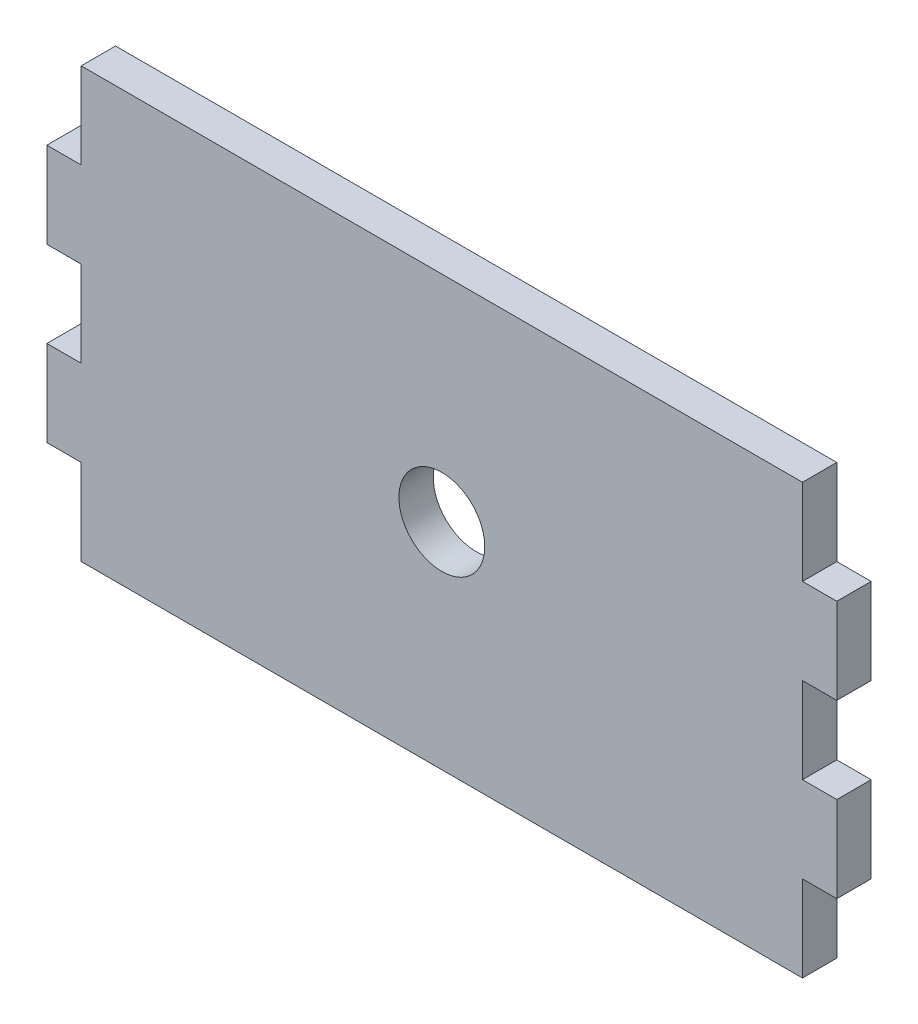
SolidWorks part; units mm, degrees
ref_plane "Front Plane" through (0, 0, 0) normal (0, 0, 1) x (1, 0, 0)
ref_plane "Top Plane" through (0, 0, 0) normal (0, 1, 0) x (1, 0, 0)
ref_plane "Right Plane" through (0, 0, 0) normal (1, 0, 0) x (0, 0, -1)
sketch "Sketch1" plane through (0, 0, 0) normal (0, 0, 1) x (1, 0, 0)
  line L0 (-46, 5) -> (-46, 15)
  line L1 (-42, -25) -> (42, -25)
  line L2 (-46, -15) -> (-46, -5)
  line L3 (-42, 25) -> (42, 25)
  line L5 (0, 25) -> (0, -25) construction
  line L6 (42, -15) -> (42, -25)
  line L7 (46, -15) -> (42, -15)
  line L8 (42, 5) -> (42, -5)
  line L9 (-46, 15) -> (-42, 15)
  line L10 (-42, 25) -> (-42, 15)
  line L11 (-46, 5) -> (-42, 5)
  line L12 (46, -5) -> (42, -5)
  line L13 (-46, -5) -> (-42, -5)
  line L14 (-42, 5) -> (-42, -5)
  line L15 (-46, -15) -> (-42, -15)
  line L16 (46, 5) -> (42, 5)
  line L17 (42, 25) -> (42, 15)
  line L18 (-42, -15) -> (-42, -25)
  line L19 (46, 15) -> (42, 15)
  line L20 (46, -15) -> (46, -5)
  line L21 (46, 5) -> (46, 15)
  circle A0 centre (0, 0) radius 5
  point P0 (0, 0)
  point P4 (0, 0)
  dimension "D1" = 84
  dimension "D2" = 4
  dimension "D3" = 10
extrude "Boss-Extrude1" add sketch "Sketch1" along normal blind 4
